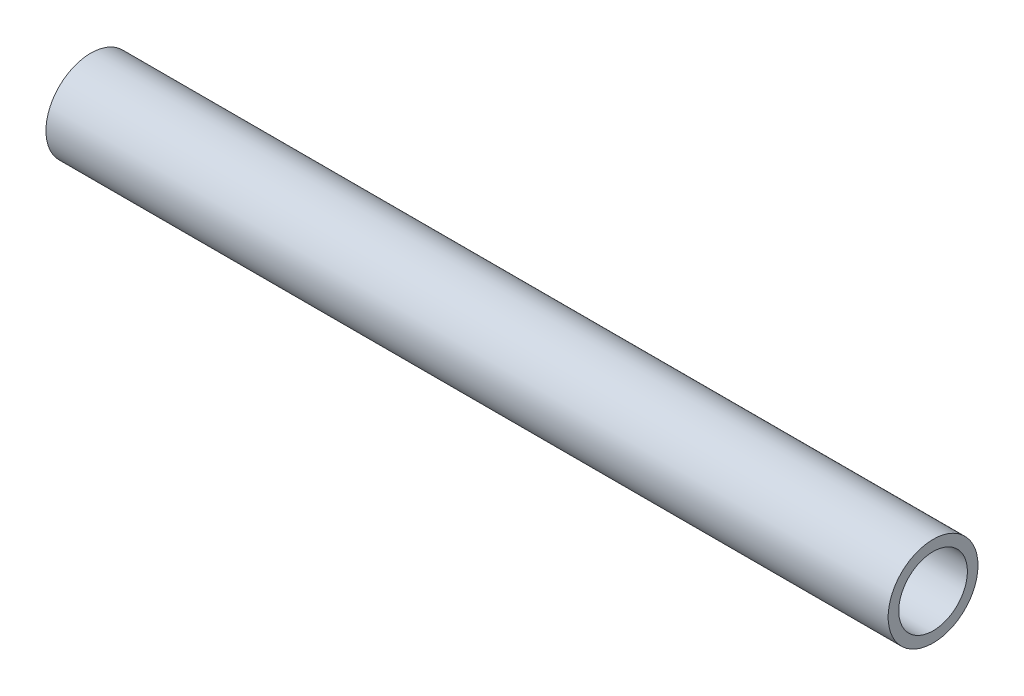
SolidWorks part; units mm, degrees
ref_plane "Front Plane" through (0, 0, 0) normal (0, 0, 1) x (1, 0, 0)
ref_plane "Top Plane" through (0, 0, 0) normal (0, 1, 0) x (1, 0, 0)
ref_plane "Right Plane" through (0, 0, 0) normal (1, 0, 0) x (0, 0, -1)
sketch "Sketch1" plane through (0, 0, 0) normal (1, 0, 0) x (0, 0, -1)
  circle A0 centre (0, 0) radius 8
  circle A1 centre (0, 0) radius 6.1148
  dimension "D1" = 16
extrude "Boss-Extrude1" add sketch "Sketch1" along normal blind 150
